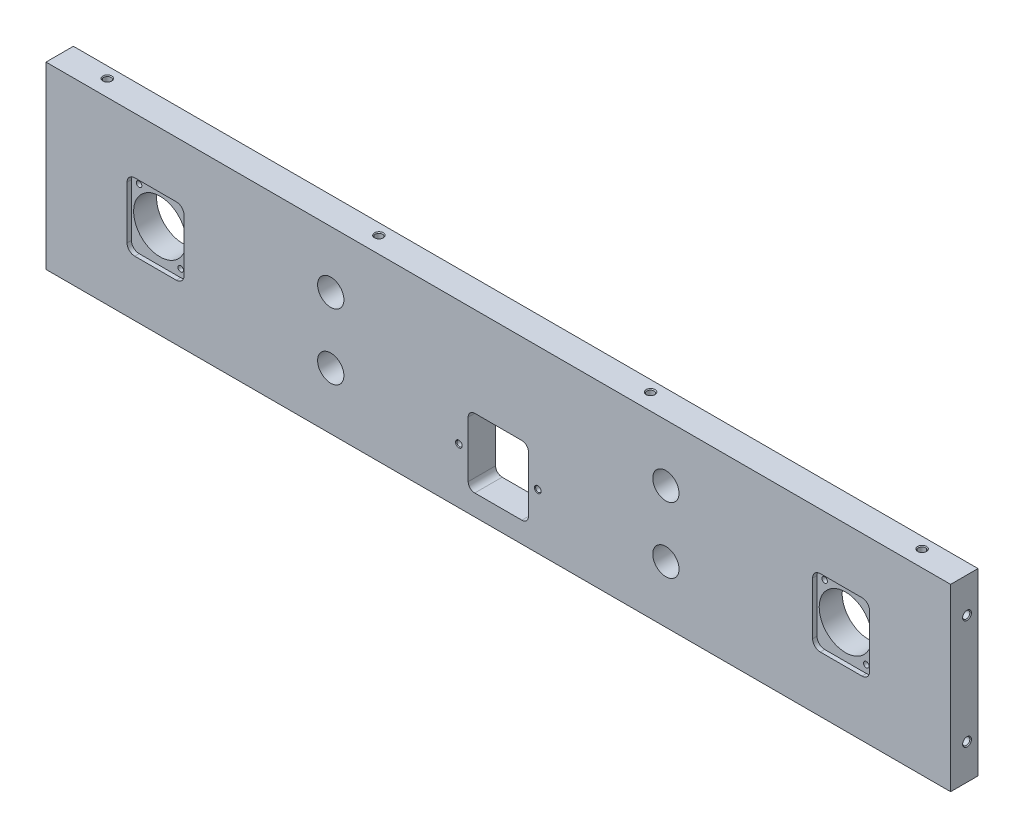
SolidWorks part; units mm, degrees
material "6061 合金"
ref_plane "前基準面" through (0, 0, 0) normal (0, 0, 1) x (1, 0, 0)
ref_plane "上基準面" through (0, 0, 0) normal (0, 1, 0) x (1, 0, 0)
ref_plane "右基準面" through (0, 0, 0) normal (1, 0, 0) x (0, 0, -1)
sketch "草圖1" plane through (0, 0, 0) normal (0, 0, 1) x (1, 0, 0)
  line L1 (0, 0) -> (413, 0)
  line L2 (0, 0) -> (0, 82)
  line L3 (0, 82) -> (413, 82)
  line L4 (413, 0) -> (413, 82)
  dimension "D1" = 413
  dimension "D2" = 82
extrude "填料-伸長1" add sketch "草圖1" along normal blind 12.5
sketch "草圖2" plane through (0, 0, 12.5) normal (0, 0, 1) x (1, 0, 0)
  line L0 (206.5, 82) -> (206.5, 0) construction
  line L1 (413, 82) -> (0, 82) construction
  line L2 (0, 0) -> (413, 0) construction
  line L3 (413, 0) -> (413, 82) construction
  line L4 (192.75, 41) -> (220.25, 41)
  line L5 (206.5, 41) -> (206.5, 9.5)
  line L6 (192.75, 9.5) -> (220.25, 9.5)
  line L7 (220.25, 41) -> (220.25, 9.5)
  line L8 (192.75, 41) -> (192.75, 9.5)
  circle A0 centre (283, 56) radius 6
  circle A1 centre (283, 26) radius 6
  circle A2 centre (363, 41) radius 12
  circle A3 centre (50, 41) radius 12
  circle A4 centre (130, 26) radius 6
  circle A5 centre (130, 56) radius 6
  dimension "D3" = 12
  dimension "D4" = 12
  dimension "D11" = 24
  dimension "D1" = 26
  dimension "D2" = 30
  dimension "D5" = 13.75
  dimension "D6" = 31.5
  dimension "D7" = 41
  dimension "D8" = 50
  dimension "D9" = 41
  dimension "D10" = 130
extrude "除料-伸長1" cut sketch "草圖2" against normal through all contours A3 | A5 | A4 | L4 L8 L6 L5 | L7 L4 L5 L6 | A0 | A1 | A2
hole_wizard "M3 螺紋孔1" positions "草圖4" profile "草圖3" tap size "M3" standard "Iso" end condition through all
sketch "草圖4" plane through (0, 0, 12.5) normal (0, 0, 1) x (1, 0, 0)
  line L0 (192.75, 41) -> (220.25, 41) construction
  line L1 (192.75, 9.5) -> (220.25, 9.5) construction
  circle A4 centre (50, 41) radius 12 construction
  circle A5 centre (363, 41) radius 12 construction
  point P0 (40.5, 53)
  point P2 (59.5, 29)
  point P4 (353.5, 53)
  point P6 (372.5, 29)
  point P8 (224.5, 25.25)
  point P10 (188.5, 25.25)
  point P14 (206.5, 41)
  dimension "D10" = 12
  dimension "D1" = 36
  dimension "D2" = 18
  dimension "D3" = 15.75
  dimension "D4" = 19
  dimension "D5" = 24
  dimension "D6" = 12
  dimension "D7" = 19
  dimension "D8" = 9.5
  dimension "D9" = 24
sketch "草圖3" plane through (40.5, 53, 12.5) normal (1, 0, 0) x (0, -1, 0)
  line L0 (0, 0) -> (0, 12.5)
  line L1 (0, 12.5) -> (1.25, 12.5)
  line L2 (1.25, 12.5) -> (1.25, 0.275)
  line L3 (1.25, 0.275) -> (1.525, 0)
  line L5 (1.525, 0) -> (0, 0)
  line L6 (-1.25, 0.275) -> (-1.525, 0) construction
  line L11 (0, -6.35) -> (0, 107.95) construction
  dimension "貫穿螺孔鑽直徑" = 2.5
  dimension "貫穿螺孔鑽深度" = 12.5
  dimension "近端錐孔直徑" = 3.05
  dimension "近端錐孔角度" = 90
cosmetic thread "鑽孔螺紋1" parameters "D2"=3
cosmetic thread "鑽孔螺紋2" parameters "D2"=3
cosmetic thread "鑽孔螺紋3" parameters "D2"=3
cosmetic thread "鑽孔螺紋4" parameters "D2"=3
cosmetic thread "鑽孔螺紋5" parameters "D2"=3
cosmetic thread "鑽孔螺紋6" parameters "D2"=3
fillet "圓角1" radius 3 4 edges at (220.25, 9.5, 6.25) (192.75, 9.5, 6.25) (220.25, 41, 6.25) (192.75, 41, 6.25)
hole_wizard "M4 螺紋孔1" positions "草圖6" profile "草圖5" tap size "M4" standard "Iso"
sketch "草圖6" plane through (0, 82, 0) normal (0, 1, 0) x (1, 0, 0)
  line L0 (0, -12.5) -> (0, 0) construction
  line L1 (413, -12.5) -> (0, -12.5) construction
  point P0 (20.5, -5)
  point P2 (144.5, -5)
  point P4 (268.5, -5)
  point P6 (392.5, -5)
  dimension "D1" = 124
  dimension "D2" = 124
  dimension "D3" = 20.5
  dimension "D4" = 124
  dimension "D5" = 7.5
sketch "草圖5" plane through (20.5, 82, 5) normal (1, 0, 0) x (0, 0, 1)
  line L0 (0, 0) -> (0, 5.9914)
  line L1 (0, 5.9914) -> (1.65, 5)
  line L2 (1.65, 5) -> (1.65, 0.375)
  line L3 (1.65, 0.375) -> (2.025, 0)
  line L5 (2.025, 0) -> (0, 0)
  line L6 (-1.65, 0.375) -> (-2.025, 0) construction
  line L10 (0, 5.9914) -> (-1.65, 5) construction
  line L11 (0, -6.35) -> (0, 107.95) construction
  dimension "螺孔鑽直徑" = 3.3
  dimension "螺孔鑽深度" = 5
  dimension "近端錐孔直徑" = 4.05
  dimension "近端錐孔角度" = 90
  dimension "導頭角度" = 118
cosmetic thread "鑽孔螺紋7" parameters "D1"=5, "D2"=4
cosmetic thread "鑽孔螺紋8" parameters "D1"=5, "D2"=4
cosmetic thread "鑽孔螺紋9" parameters "D1"=5, "D2"=4
cosmetic thread "鑽孔螺紋10" parameters "D1"=5, "D2"=4
hole_wizard "M4 螺紋孔2" positions "草圖8" profile "草圖7" tap size "M4" standard "Iso"
sketch "草圖8" plane through (0, 0, 0) normal (0, -1, 0) x (-1, 0, 0)
  line L0 (0, -12.5) -> (0, 0) construction
  line L2 (0, -12.5) -> (-413, -12.5) construction
  point P0 (-144.5, -5)
  point P1 (-20.5, -5)
  point P3 (-268.5, -5)
  point P5 (-392.5, -5)
  dimension "D1" = 20.5
  dimension "D2" = 124
  dimension "D3" = 124
  dimension "D4" = 124
  dimension "D5" = 7.5
sketch "草圖7" plane through (144.5, 0, 5) normal (1, 0, 0) x (0, 0, -1)
  line L0 (0, 0) -> (0, 5.9914)
  line L1 (0, 5.9914) -> (1.65, 5)
  line L2 (1.65, 5) -> (1.65, 0.375)
  line L3 (1.65, 0.375) -> (2.025, 0)
  line L5 (2.025, 0) -> (0, 0)
  line L6 (-1.65, 0.375) -> (-2.025, 0) construction
  line L10 (0, 5.9914) -> (-1.65, 5) construction
  line L11 (0, -6.35) -> (0, 107.95) construction
  dimension "螺孔鑽直徑" = 3.3
  dimension "螺孔鑽深度" = 5
  dimension "近端錐孔直徑" = 4.05
  dimension "近端錐孔角度" = 90
  dimension "導頭角度" = 118
cosmetic thread "鑽孔螺紋11" parameters "D1"=5, "D2"=4
cosmetic thread "鑽孔螺紋12" parameters "D1"=5, "D2"=4
cosmetic thread "鑽孔螺紋13" parameters "D1"=5, "D2"=4
cosmetic thread "鑽孔螺紋14" parameters "D1"=5, "D2"=4
hole_wizard "M4 螺紋孔3" positions "草圖12" profile "草圖11" tap size "M4" standard "Iso"
sketch "草圖12" plane through (0, 0, 0) normal (-1, 0, 0) x (0, 0, 1)
  line L0 (12.5, 82) -> (0, 82) construction
  line L3 (12.5, 82) -> (12.5, 0) construction
  point P0 (5, 66)
  point P2 (5, 16)
  point P5 (6.25, 82)
  dimension "D1" = 50
  dimension "D2" = 16
  dimension "D3" = 7.5
sketch "草圖11" plane through (0, 66, 5) normal (0, 1, 0) x (0, 0, 1)
  line L0 (0, 0) -> (0, 11.0914)
  line L1 (0, 11.0914) -> (1.65, 10.1)
  line L2 (1.65, 10.1) -> (1.65, 0.375)
  line L3 (1.65, 0.375) -> (2.025, 0)
  line L5 (2.025, 0) -> (0, 0)
  line L6 (-1.65, 0.375) -> (-2.025, 0) construction
  line L10 (0, 11.0914) -> (-1.65, 10.1) construction
  line L11 (0, -6.35) -> (0, 107.95) construction
  dimension "螺孔鑽直徑" = 3.3
  dimension "螺孔鑽深度" = 10.1
  dimension "近端錐孔直徑" = 4.05
  dimension "近端錐孔角度" = 90
  dimension "導頭角度" = 118
cosmetic thread "鑽孔螺紋15" parameters "D1"=8, "D2"=4
cosmetic thread "鑽孔螺紋16" parameters "D1"=8, "D2"=4
hole_wizard "M4 螺紋孔4" positions "草圖14" profile "草圖13" tap size "M4" standard "Iso"
sketch "草圖14" plane through (413, 0, 0) normal (1, 0, 0) x (0, 0, -1)
  line L0 (-12.5, 82) -> (0, 82) construction
  line L1 (-12.5, 0) -> (-12.5, 82) construction
  point P0 (-5, 66)
  point P2 (-5, 16)
  dimension "D1" = 16
  dimension "D2" = 50
  dimension "D3" = 7.5
sketch "草圖13" plane through (413, 66, 5) normal (0, 1, 0) x (0, 0, -1)
  line L0 (0, 0) -> (0, 11.0914)
  line L1 (0, 11.0914) -> (1.65, 10.1)
  line L2 (1.65, 10.1) -> (1.65, 0.375)
  line L3 (1.65, 0.375) -> (2.025, 0)
  line L5 (2.025, 0) -> (0, 0)
  line L6 (-1.65, 0.375) -> (-2.025, 0) construction
  line L10 (0, 11.0914) -> (-1.65, 10.1) construction
  line L11 (0, -6.35) -> (0, 107.95) construction
  dimension "螺孔鑽直徑" = 3.3
  dimension "螺孔鑽深度" = 10.1
  dimension "近端錐孔直徑" = 4.05
  dimension "近端錐孔角度" = 90
  dimension "導頭角度" = 118
cosmetic thread "鑽孔螺紋17" parameters "D1"=8, "D2"=4
cosmetic thread "鑽孔螺紋18" parameters "D1"=8, "D2"=4
sketch "草圖15" plane through (0, 0, 0) normal (0, 0, -1) x (-1, 0, 0)
  circle A0 centre (-283, 56) radius 12.5
  circle A1 centre (-283, 26) radius 12.5
  circle A2 centre (-130, 56) radius 12.5
  circle A3 centre (-130, 26) radius 12.5
  circle A4 centre (-130, 56) radius 6 construction
  circle A5 centre (-130, 26) radius 6 construction
  circle A6 centre (-283, 56) radius 6 construction
  circle A7 centre (-283, 26) radius 6 construction
  dimension "D1" = 25
  dimension "D2" = 25
  dimension "D3" = 25
  dimension "D4" = 25
extrude "除料-伸長2" cut sketch "草圖15" against normal blind 3
sketch "草圖16" plane through (0, 0, 12.5) normal (0, 0, 1) x (1, 0, 0)
  line L1 (37, 25.5) -> (63, 25.5)
  line L2 (37, 25.5) -> (37, 56.5)
  line L3 (37, 56.5) -> (63, 56.5)
  line L4 (63, 25.5) -> (63, 56.5)
  line L5 (37, 25.5) -> (63, 56.5) construction
  line L6 (37, 56.5) -> (63, 25.5) construction
  line L7 (350, 25.5) -> (376, 25.5)
  line L8 (350, 25.5) -> (350, 56.5)
  line L9 (350, 56.5) -> (376, 56.5)
  line L10 (376, 25.5) -> (376, 56.5)
  line L11 (350, 25.5) -> (376, 56.5) construction
  line L12 (350, 56.5) -> (376, 25.5) construction
  point P0 (50, 41)
  point P6 (363, 41)
  dimension "D1" = 31
  dimension "D2" = 26
  dimension "D3" = 26
  dimension "D4" = 31
extrude "除料-伸長3" cut sketch "草圖16" against normal blind 2
fillet "圓角2" radius 3.5 8 edges at (376, 25.5, 11.5) (376, 56.5, 11.5) (350, 56.5, 11.5) (350, 25.5, 11.5) (37, 25.5, 11.5) (63, 25.5, 11.5) (63, 56.5, 11.5) (37, 56.5, 11.5)
